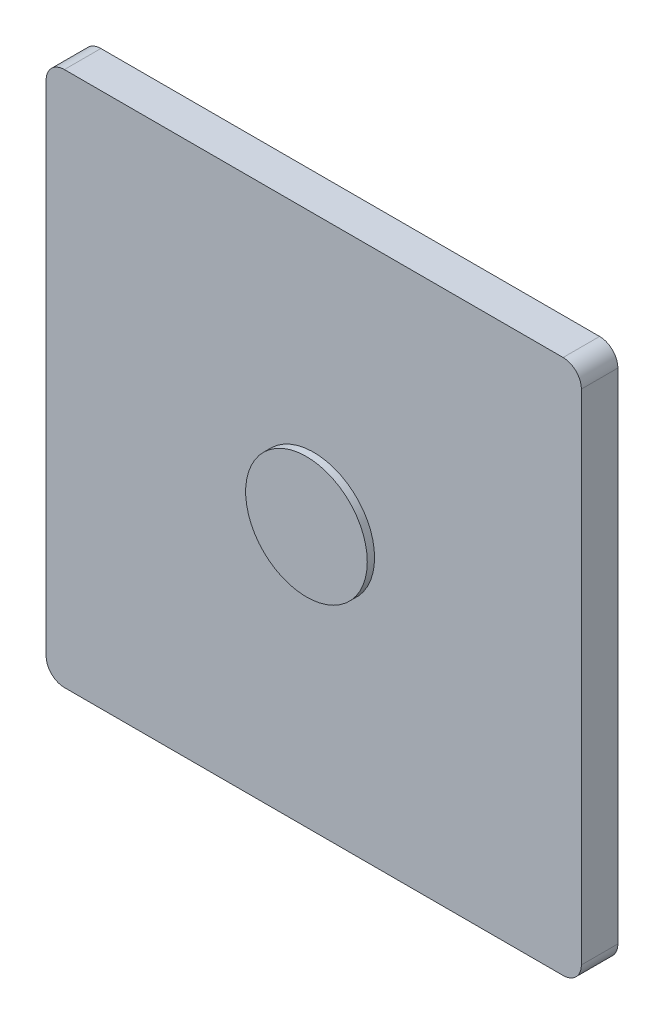
SolidWorks part; units mm, degrees
ref_plane "Plano frontal" through (0, 0, 0) normal (0, 0, 1) x (1, 0, 0)
ref_plane "Plano superior" through (0, 0, 0) normal (0, 1, 0) x (1, 0, 0)
ref_plane "Plano direito" through (0, 0, 0) normal (1, 0, 0) x (0, 0, -1)
sketch "Esboço4" plane through (0, 0, 0) normal (0, 0, 1) x (1, 0, 0)
  line L0 (0, 25) -> (0, 22) construction
  line L1 (-25, 0) -> (-22, 0) construction
  line L2 (-22, 0) -> (-22, 20.5)
  line L3 (0, 22) -> (20.5, 22)
  line L4 (22, 20.5) -> (22, 0)
  line L5 (25, 0) -> (22, 0) construction
  line L6 (0, 25) -> (0, 22) construction
  line L7 (25, 25) -> (0, 25) construction
  line L8 (25, 0) -> (25, 25) construction
  line L9 (-25, 25) -> (-25, 0) construction
  line L10 (0, 25) -> (-25, 25) construction
  line L11 (0, 25) -> (0, 0) construction
  line L12 (25, 0) -> (0, 0) construction
  line L13 (0, 0) -> (0, 25) construction
  line L14 (0, 0) -> (-25, 0) construction
  line L15 (22, 0) -> (22, -20.5)
  line L16 (20.5, -22) -> (0, -22)
  line L17 (-20.5, 22) -> (0, 22)
  line L18 (0, -25) -> (0, -22) construction
  line L19 (25, 0) -> (22, 0) construction
  line L20 (25, -25) -> (25, 0) construction
  line L21 (0, -25) -> (25, -25) construction
  line L22 (0, -25) -> (0, 0) construction
  line L23 (0, 0) -> (25, 0) construction
  line L24 (0, -22) -> (-20.5, -22)
  line L25 (-22, -20.5) -> (-22, 0)
  line L26 (-25, 0) -> (-22, 0) construction
  line L27 (0, -25) -> (0, -22) construction
  line L28 (-25, -25) -> (0, -25) construction
  line L29 (-25, 0) -> (-25, -25) construction
  line L30 (-25, 0) -> (0, 0) construction
  line L31 (0, 0) -> (0, -25) construction
  arc A0 (-20.5, 22) -> (-22, 20.5) centre (-20.5, 20.5) ccw
  arc A2 (22, 20.5) -> (20.5, 22) centre (20.5, 20.5) ccw
  arc A4 (20.5, -22) -> (22, -20.5) centre (20.5, -20.5) ccw
  arc A6 (-22, -20.5) -> (-20.5, -22) centre (-20.5, -20.5) ccw
  point P12 (0, 0)
  point P22 (-22, -22)
  point P25 (-22, 22)
  point P26 (0, 0)
  point P29 (-22, 22)
  point P40 (0, 0)
  point P43 (22, 22)
  point P53 (0, 0)
  point P56 (22, -22)
  point P57 (0, 0)
  dimension "D1" = 4
extrude "Ressalto-extrusão1" add sketch "Esboço4" along normal blind 3
sketch "Esboço5" plane through (0, 0, 3) normal (0, 0, 1) x (1, 0, 0)
  circle A0 centre (0, 0) radius 5
extrude "Ressalto-extrusão2" add sketch "Esboço5" along normal blind 0.6
